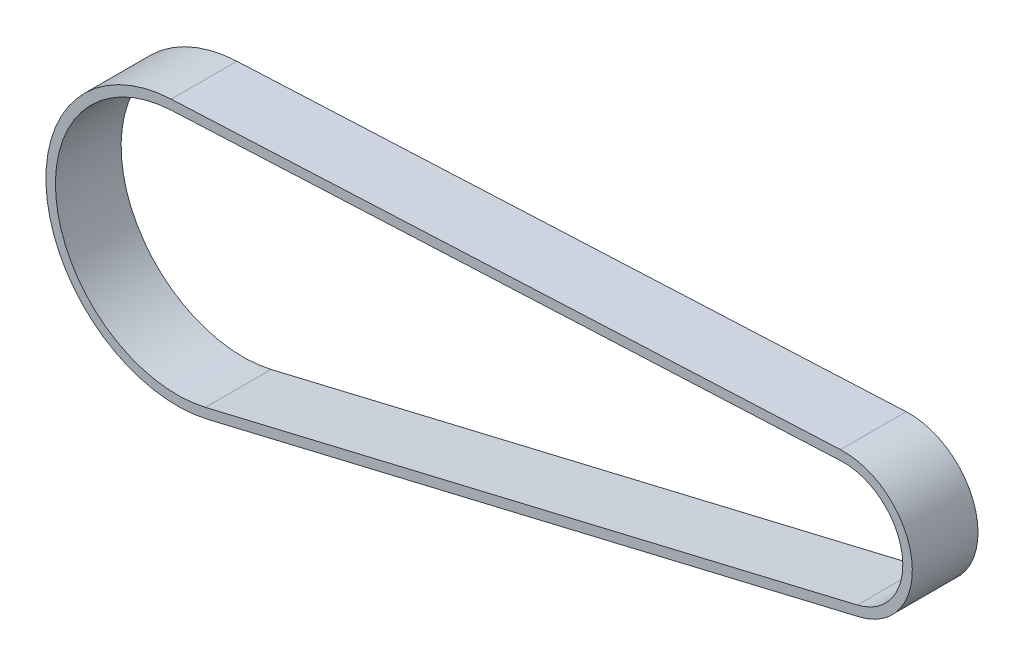
SolidWorks part; units mm, degrees
material "Rubber"
ref_plane "Front Plane" through (0, 0, 0) normal (0, 0, 1) x (1, 0, 0)
ref_plane "Top Plane" through (0, 0, 0) normal (0, 1, 0) x (1, 0, 0)
ref_plane "Right Plane" through (0, 0, 0) normal (1, 0, 0) x (0, 0, -1)
sketch "Sketch2" plane through (0, 0, 0) normal (0, 0, 1) x (1, 0, 0)
  line L0 (0, 0) -> (1, 0) construction
  line L1 (0, 0) -> (0, 1) construction
  line L2 (-28.9855, -7.0181) -> (-97.464, -23.2767)
  line L3 (-101.293, 3.9351) -> (-30.987, 7.2054)
  arc A0 (-30.987, 7.2054) -> (-28.9855, -7.0181) centre (-30.6518, 0) cw
  arc A1 (-97.464, -23.2767) -> (-101.293, 3.9351) centre (-100.6518, -9.85) cw
extrude "Extrude-Thin1" add sketch "Sketch2" along normal up to surface (6.9 mm away) thin
